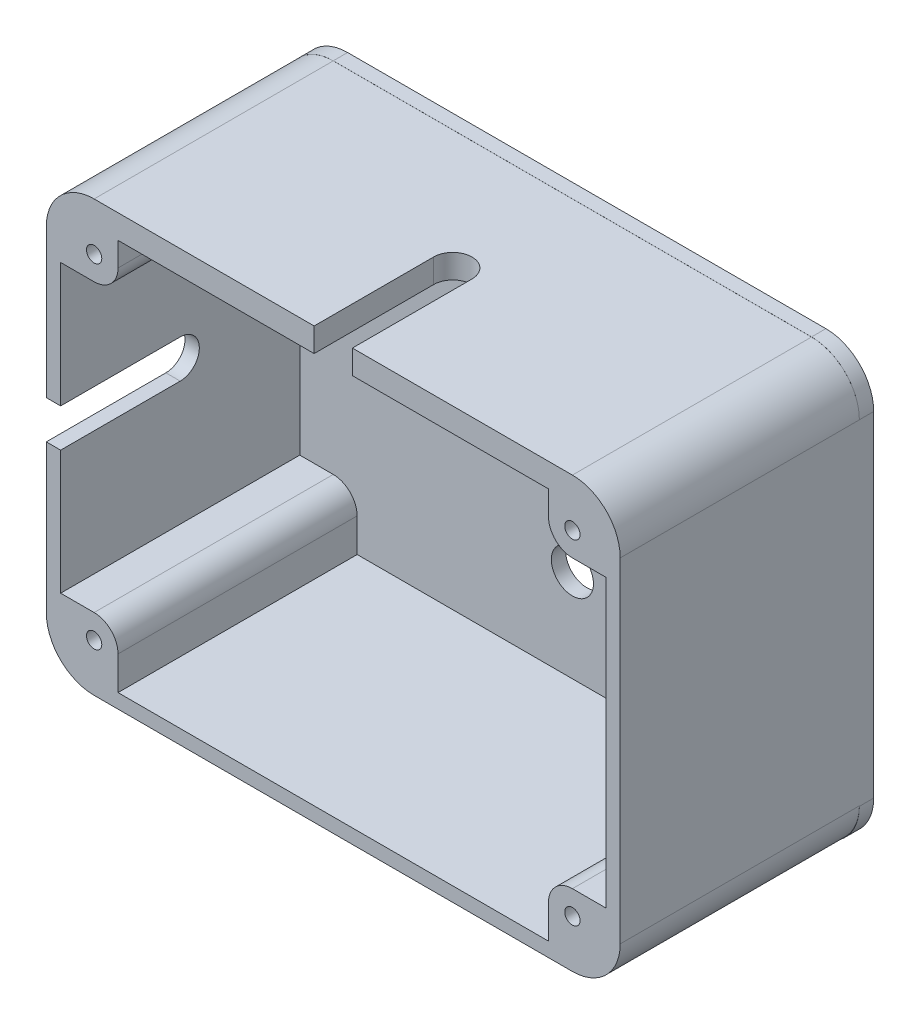
SolidWorks part; units mm, degrees
ref_plane "Front Plane" through (0, 0, 0) normal (0, 0, 1) x (1, 0, 0)
ref_plane "Top Plane" through (0, 0, 0) normal (0, 1, 0) x (1, 0, 0)
ref_plane "Right Plane" through (0, 0, 0) normal (1, 0, 0) x (0, 0, -1)
sketch "Sketch1" plane through (0, 0, 0) normal (0, 0, 1) x (1, 0, 0)
  line L0 (60, 0) -> (-60, 0) construction
  line L1 (-50, 45) -> (50, 45)
  line L2 (-60, 35) -> (-60, -35)
  line L3 (-50, -45) -> (50, -45)
  line L4 (60, 35) -> (60, -35)
  line L5 (-60, 45) -> (60, -45) construction
  line L6 (-60, -45) -> (60, 45) construction
  line L7 (0, 45) -> (0, -45) construction
  arc A0 (-60, -35) -> (-50, -45) centre (-50, -35) ccw
  arc A1 (50, -45) -> (60, -35) centre (50, -35) ccw
  arc A2 (60, 35) -> (50, 45) centre (50, 35) ccw
  arc A3 (-50, 45) -> (-60, 35) centre (-50, 35) ccw
  circle A4 centre (0, 22.5) radius 4.4
  circle A5 centre (0, -22.5) radius 4.4
  point P0 (0, 0)
  dimension "D3" = 10
  dimension "D4" = 22.5
  dimension "D1" = 120
  dimension "D2" = 90
  dimension "D5" = 22.5
extrude "Boss-Extrude1" add sketch "Sketch1" along normal blind 3
sketch "Sketch2" plane through (0, -44.9029, 3) normal (0, 0, 1) x (1, 0, 0)
  line L0 (-50, 0) -> (50, 0)
  line L1 (-45, 10) -> (-45, 3)
  line L2 (-50, 15) -> (-57, 15)
  line L3 (60, 10) -> (60, 79.8877)
  line L4 (50, 89.8877) -> (-50, 89.8877)
  line L5 (-60, 79.8877) -> (-60, 10)
  line L6 (-45, 3) -> (45, 3)
  line L7 (57, 15) -> (57, 74.8877)
  line L8 (45, 84.8877) -> (-45, 84.8877)
  line L9 (-57, 74.8877) -> (-57, 15)
  line L10 (-45, 79.8877) -> (-45, 84.8877)
  line L11 (-50, 74.8877) -> (-57, 74.8877)
  line L12 (45, 10) -> (45, 3)
  line L13 (50, 15) -> (57, 15)
  line L14 (45, 79.8877) -> (45, 84.8877)
  line L15 (50, 74.8877) -> (57, 74.8877)
  arc A0 (-60, 10) -> (-50, 0) centre (-50, 10) ccw
  arc A1 (60, 10) -> (50, 0) centre (50, 10) cw
  arc A2 (60, 79.8877) -> (50, 89.8877) centre (50, 79.8877) ccw
  arc A3 (-50, 89.8877) -> (-60, 79.8877) centre (-50, 79.8877) ccw
  arc A9 (50, 15) -> (45, 10) centre (50, 10) ccw
  arc A10 (45, 79.8877) -> (50, 74.8877) centre (50, 79.8877) ccw
  arc A11 (-50, 74.8877) -> (-45, 79.8877) centre (-50, 79.8877) ccw
  arc A12 (55, 79.8877) -> (50, 84.8877) centre (50, 79.8877) ccw construction
  arc A13 (-45, 10) -> (-50, 15) centre (-50, 10) ccw
  arc A14 (55, 10) -> (50, 5) centre (50, 10) cw construction
  arc A15 (-55, 10) -> (-50, 5) centre (-50, 10) ccw construction
  arc A16 (-50, 84.8877) -> (-55, 79.8877) centre (-50, 79.8877) ccw construction
  circle A17 centre (-50, 79.8877) radius 1.6
  circle A18 centre (-50, 10) radius 1.6
  circle A19 centre (50, 10) radius 1.6
  circle A20 centre (50, 79.8877) radius 1.6
  dimension "D1" = 3
  dimension "D2" = 5
  dimension "D3" = 3
  dimension "D4" = 3
extrude "Boss-Extrude2" add sketch "Sketch2" along normal blind 50
sketch "Sketch4" plane through (0, -44.9029, 53) normal (0, 0, 1) x (1, 0, 0)
  line L1 (-50, 0.202) -> (50, 0.202)
  line L2 (-60, 10.202) -> (-60, 80)
  line L3 (-50, 90) -> (50, 90)
  line L4 (60, 10.202) -> (60, 80)
  arc A0 (-50, 0.202) -> (-60, 10.202) centre (-50, 10.202) cw
  arc A1 (50, 0.202) -> (60, 10.202) centre (50, 10.202) ccw
  arc A2 (60, 80) -> (50, 90) centre (50, 80) ccw
  arc A3 (-50, 90) -> (-60, 80) centre (-50, 80) ccw
  circle A4 centre (-50, 79.8877) radius 1.9
  circle A5 centre (50, 79.8877) radius 1.9
  circle A6 centre (50, 10) radius 1.9
  circle A7 centre (-50, 10) radius 1.9
  point P8 (-60, 0.202)
sketch "Sketch6" plane through (0, 44.9848, 0) normal (0, 1, 0) x (1, 0, 0)
  line L0 (-4, -28) -> (-4, -53)
  line L1 (-50, -53) -> (50, -53) construction
  line L2 (4, -28) -> (4, -53)
  line L3 (-4, -53) -> (4, -53)
  arc A0 (4, -28) -> (-4, -28) centre (0, -28) ccw
extrude "Cut-Extrude1" cut sketch "Sketch6" against normal blind 10
sketch "Sketch7" plane through (-60, 0, 0) normal (-1, 0, 0) x (0, 0, 1)
  line L0 (28, 4) -> (53, 4)
  line L1 (53, -34.7009) -> (53, 35.0971) construction
  line L2 (28, -4) -> (53, -4)
  line L3 (53, -4) -> (53, 4)
  arc A0 (28, 4) -> (28, -4) centre (28, 0) ccw
extrude "Cut-Extrude2" cut sketch "Sketch7" against normal blind 10
